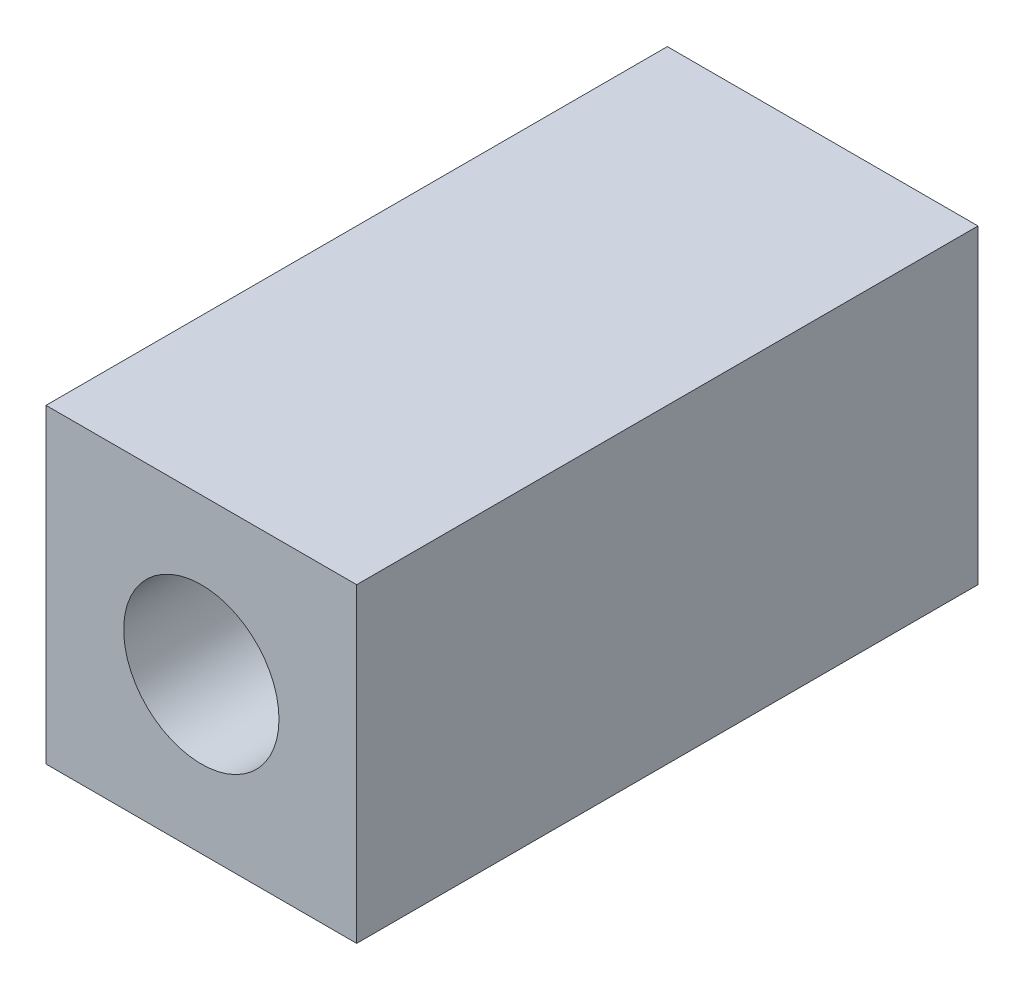
SolidWorks part; units mm, degrees
ref_plane "Front Plane" through (0, 0, 0) normal (0, 0, 1) x (1, 0, 0)
ref_plane "Top Plane" through (0, 0, 0) normal (0, 1, 0) x (1, 0, 0)
ref_plane "Right Plane" through (0, 0, 0) normal (1, 0, 0) x (0, 0, -1)
sketch "Sketch1" plane through (0, 0, 0) normal (0, 0, 1) x (1, 0, 0)
  line L0 (5, 0) -> (5, -10) construction
  line L1 (0, 0) -> (10, 0)
  line L2 (0, 0) -> (0, -10)
  line L3 (0, -10) -> (10, -10)
  line L4 (10, 0) -> (10, -10)
  circle A0 centre (5, -5) radius 2.5
  dimension "D1" = 10
  dimension "D2" = 10
extrude "Boss-Extrude1" add sketch "Sketch1" along normal blind 20
